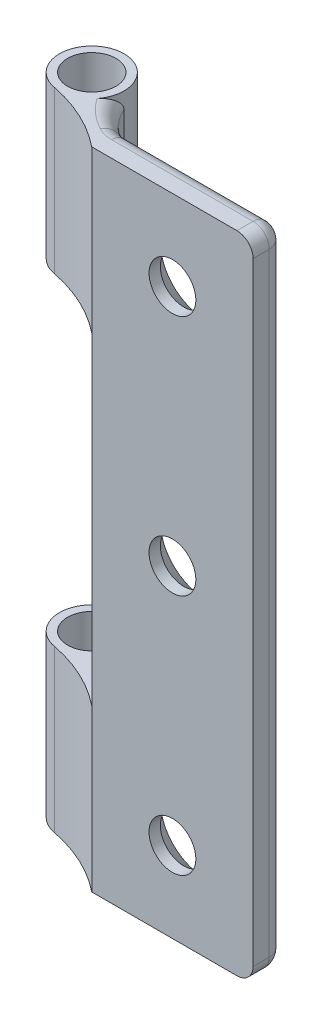
SolidWorks part; units mm, degrees
ref_plane "Front Plane" through (0, 0, 0) normal (0, 0, 1) x (1, 0, 0)
ref_plane "Top Plane" through (0, 0, 0) normal (0, 1, 0) x (1, 0, 0)
ref_plane "Right Plane" through (0, 0, 0) normal (1, 0, 0) x (0, 0, -1)
sketch "Sketch3" plane through (0, 0, 0) normal (0, 1, 0) x (1, 0, 0)
  line L1 (-5, 1) -> (5, 1)
  line L3 (-5, -1) -> (5, -1)
  line L4 (5, 1) -> (5, -1)
  line L5 (-5, 1) -> (5, -1) construction
  line L6 (-5, -1) -> (5, 1) construction
  arc A1 (-7, 3) -> (-9.3322, 1.0278) centre (-9, 3) ccw
  circle A2 centre (-9, 3) radius 1.5
  arc A3 (-9.3322, 1.0278) -> (-5, -1) centre (-11.2824, -8.7802) cw
  arc A4 (-5, 1) -> (-7, 3) centre (-3.3542, 4.6458) cw
  point P0 (0, 0)
  dimension "D3" = 4
  dimension "D4" = 3
  dimension "D7" = 4
  dimension "D8" = 10
  dimension "D1" = 2
  dimension "D2" = 10
  dimension "D5" = 2
  dimension "D6" = 4
extrude "Boss-Extrude2" add sketch "Sketch3" along normal blind 40
sketch "Sketch4" plane through (0, 0, 0) normal (0, 0, 1) x (1, 0, 0)
  line L0 (-11, 40) -> (-11, 0) construction
  line L1 (-5, 40) -> (-5, 0) construction
  line L2 (-11, 40) -> (-11, 0)
  line L3 (-5, 40) -> (-5, 0)
  line L4 (-11, 30) -> (-5, 30)
  line L5 (-5, 30) -> (-5, 10)
  line L6 (-5, 10) -> (-11, 10)
  line L7 (-11, 10) -> (-11, 30)
  line L8 (-9.3322, 0) -> (-5, 0) construction
  dimension "D1" = 10
  dimension "D2" = 20
extrude "Cut-Extrude1" cut sketch "Sketch4" against normal blind 200 and the other way blind 40 contours L6 L3 L4 L2
sketch "Sketch5" plane through (0, 0, -1) normal (0, 0, -1) x (-1, 0, 0)
  line L0 (0, 40) -> (0, 0) construction
  line L1 (5, 35) -> (-5, 35) construction
  line L2 (5, 5) -> (-5, 5) construction
  line L6 (-5, 0) -> (5, 0)
  line L7 (5, 0) -> (5, 10)
  line L8 (5, 10) -> (5, 30)
  line L9 (5, 30) -> (5, 40)
  line L10 (5, 40) -> (-5, 40)
  line L11 (-5, 40) -> (-5, 0)
  line L12 (-5, 0) -> (5, 0)
  line L13 (5, 0) -> (5, 10)
  line L14 (5, 10) -> (5, 30)
  line L15 (5, 30) -> (5, 40)
  line L16 (5, 40) -> (-5, 40)
  line L17 (-5, 40) -> (-5, 0)
  circle A0 centre (0, 35) radius 2
  circle A1 centre (0, 5) radius 2
  circle A2 centre (0, 20) radius 2
  dimension "D2" = 4
  dimension "D3" = 4
  dimension "D4" = 4
  dimension "D1" = 0
fillet "Fillet1" radius 1 2 edges at (-5, 20, -1) (5, 20, -1)
fillet "Fillet2" radius 1 10 edges at (-6.1827, 0, -1.8173) (-6.1827, 40, -1.8173) (5, 0, 0.5) (4.7071, 0, -0.7071) (5, 40, 0.5) (4.7071, 40, -0.7071) (-5, 5, -1) (-5, 35, -1) (-0.5, 0, -1) (-0.5, 40, -1)
hole_wizard "CSK for M2.5 Countersunk Flat Head Screw1" positions "3DSketch2" profile "Sketch6" countersink size "M2.5" standard "ISO" end condition through all
sketch3d "3DSketch2"
  point P0 (0, 35, -1)
  point P3 (0, 20, -1)
  point P6 (0, 5, -1)
sketch "Sketch6" plane through (0, 35, -1) normal (1, 0, 0) x (0, 1, 0)
  line L0 (0, 0) -> (0, 2)
  line L1 (0, 2) -> (1.45, 2)
  line L2 (1.45, 2) -> (1.45, 1.3)
  line L3 (1.45, 1.3) -> (2.75, 0)
  line L5 (2.75, 0) -> (0, 0)
  line L6 (-1.45, 1.3) -> (-2.75, 0) construction
  line L11 (0, -6.35) -> (0, 107.95) construction
  dimension "Thru Hole Dia." = 2.9
  dimension "Thru Hole Depth" = 2
  dimension "Near C'Sink Dia." = 5.5
  dimension "Near C'Sink Angle" = 90
